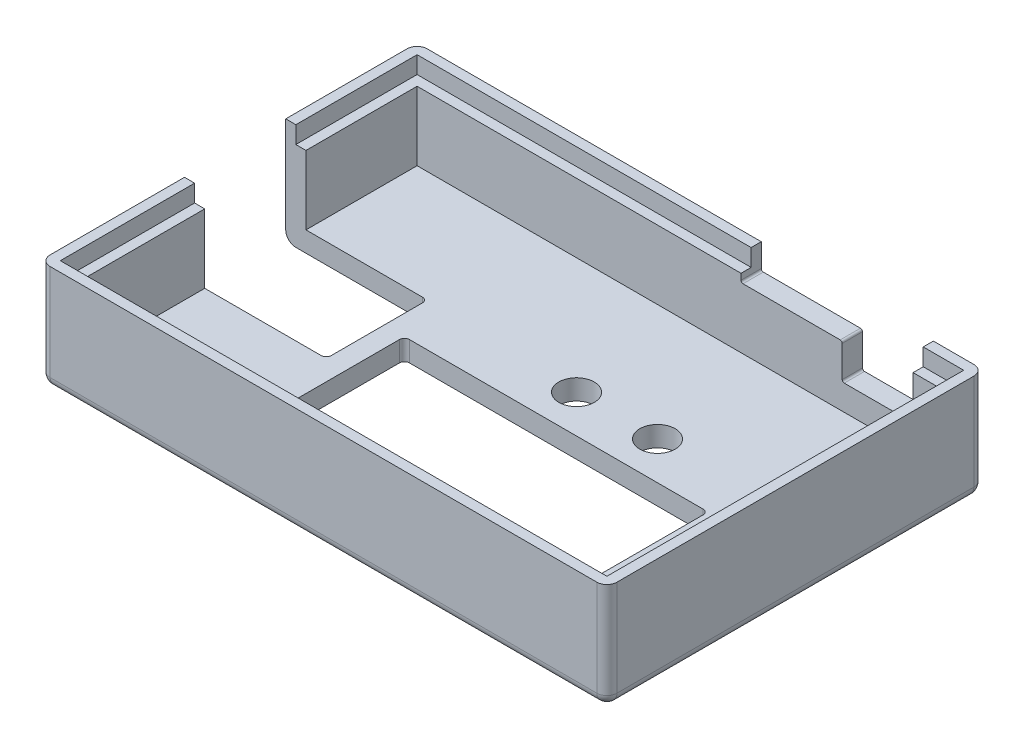
SolidWorks part; units mm, degrees
ref_plane "Front Plane" through (0, 0, 0) normal (0, 0, 1) x (1, 0, 0)
ref_plane "Top Plane" through (0, 0, 0) normal (0, 1, 0) x (1, 0, 0)
ref_plane "Right Plane" through (0, 0, 0) normal (1, 0, 0) x (0, 0, -1)
sketch "Sketch1" plane through (0, 0, 0) normal (0, 1, 0) x (1, 0, 0)
  line L0 (0, 0) -> (56, 0)
  line L1 (56, 0) -> (56, 37.25)
  line L2 (56, 37.25) -> (0, 37.25)
  line L3 (0, 37.25) -> (0, 0)
  dimension "D1" = 56
  dimension "D2" = 37.25
extrude "Boss-Extrude1" add sketch "Sketch1" along normal blind 2
sketch "Sketch2" plane through (0, 2, 0) normal (0, 1, 0) x (1, 0, 0)
  line L0 (2, 35.25) -> (2, 2)
  line L1 (2, 2) -> (54, 2)
  line L2 (0, 37.25) -> (0, 0) construction
  line L3 (0, 0) -> (56, 0) construction
  line L4 (2, 35.25) -> (54, 35.25)
  line L5 (54, 35.25) -> (54, 2)
  line L6 (56, 0) -> (56, 37.25) construction
  line L7 (56, 37.25) -> (0, 37.25) construction
  line L12 (0, 37.25) -> (0, 0)
  line L13 (0, 0) -> (56, 0)
  line L14 (56, 0) -> (56, 37.25)
  line L15 (56, 37.25) -> (0, 37.25)
  line L16 (0, 37.25) -> (0, 0)
  line L17 (0, 0) -> (56, 0)
  line L18 (56, 0) -> (56, 37.25)
  line L19 (56, 37.25) -> (0, 37.25)
  dimension "D1" = 2
  dimension "D2" = 2
  dimension "D3" = 2
  dimension "D4" = 2
  dimension "D5" = 0
extrude "Boss-Extrude2" add sketch "Sketch2" along normal blind 8.5
sketch "Sketch3" plane through (0, 2, 0) normal (0, 1, 0) x (1, 0, 0)
  line L0 (54, 2) -> (54, 35.25) construction
  line L4 (2, 18.625) -> (54, 18.625) construction
  line L5 (2, 35.25) -> (2, 2) construction
  line L6 (12, 6) -> (48, 6) construction
  line L7 (12, 32) -> (12, 6) construction
  circle A0 centre (12, 32) radius 1.6
  circle A1 centre (12, 6) radius 1.6
  circle A2 centre (48, 6) radius 1.6
  circle A6 centre (48, 6) radius 1.5 construction
  circle A7 centre (12, 6) radius 1.5 construction
  circle A8 centre (12, 32) radius 1.5 construction
  circle A9 centre (48, 6) radius 2 construction
  circle A10 centre (12, 6) radius 2 construction
  circle A11 centre (12, 32) radius 2 construction
sketch "Sketch5" plane through (0, 10.5, 0) normal (0, 1, 0) x (1, 0, 0)
  line L0 (1, 1) -> (55, 1)
  line L1 (0, 0) -> (56, 0) construction
  line L2 (55, 1) -> (55, 36.25)
  line L3 (55, 36.25) -> (1, 36.25)
  line L4 (1, 36.25) -> (1, 1)
  line L5 (56, 0) -> (56, 37.25) construction
  line L6 (56, 37.25) -> (0, 37.25) construction
  line L7 (0, 37.25) -> (0, 0) construction
  line L8 (0, 37.25) -> (0, 0)
  line L9 (56, 37.25) -> (0, 37.25)
  line L10 (56, 0) -> (56, 37.25)
  line L11 (0, 0) -> (56, 0)
  line L12 (54, 2) -> (54, 35.25) construction
  line L13 (54, 35.25) -> (2, 35.25) construction
  line L14 (2, 35.25) -> (2, 2) construction
  line L15 (2, 2) -> (54, 2) construction
  line L16 (54, 2) -> (54, 35.25)
  line L17 (54, 35.25) -> (2, 35.25)
  line L18 (2, 35.25) -> (2, 2)
  line L19 (2, 2) -> (54, 2)
  line M9 (2, 2) -> (2, 35.25)
  line M10 (2, 35.25) -> (54, 35.25)
  line M11 (54, 35.25) -> (54, 2)
  line M12 (54, 2) -> (2, 2)
  dimension "D1" = 1
  dimension "D2" = 1
  dimension "D3" = 1
  dimension "D4" = 1
extrude "Cut-Extrude1" cut sketch "Sketch5" against normal blind 1 contours L3 L4 L0 L2 M12 M9 M10 M11 | L18 L19 L16 L17
fillet "Fillet1" radius 1 4 edges at (56, 5.25, -37.25) (56, 5.25, 0) (0, 5.25, -37.25) (0, 5.25, 0)
extrude "Cut-Extrude2" [suppressed] cut sketch "Sketch3" against normal blind 10
sketch "Sketch7" plane through (0, 2, 0) normal (0, 1, 0) x (1, 0, 0)
  line L0 (16, 6) -> (46, 6)
  line L1 (46, 6) -> (46, 20)
  line L2 (16, 6) -> (16, 20)
  line L3 (16, 20) -> (46, 20)
  line L4 (54, 2) -> (54, 35.25) construction
  line L6 (2, 2) -> (54, 2) construction
  dimension "D1" = 14
  dimension "D2" = 30
  dimension "D3" = 8
  dimension "D4" = 4
extrude "Cut-Extrude3" cut sketch "Sketch7" against normal blind 10
sketch "Sketch8" plane through (0, 0, 0) normal (0, -1, 0) x (1, 0, 0)
  circle A0 centre (29.25, -23.75) radius 1.75
  circle A1 centre (37.25, -23.75) radius 1.75
extrude "Cut-Extrude4" cut sketch "Sketch8" against normal blind 10
sketch "Sketch9" plane through (0, 0, -37.25) normal (0, 0, -1) x (-1, 0, 0)
  line L0 (-44, 4.5) -> (-44, 10.5)
  line L1 (-44, 10.5) -> (-51, 10.5)
  line L2 (-51, 10.5) -> (-51, 4.5)
  line L3 (-51, 4.5) -> (-44, 4.5)
  line L4 (-55, 10.5) -> (-55, 0) construction
  line L5 (-55, 10.5) -> (-1, 10.5) construction
  point P5 (-55, 5.25)
  dimension "D1" = 7
  dimension "D2" = 6
  dimension "D3" = 4
  dimension "D4" = 0
extrude "Cut-Extrude5" cut sketch "Sketch9" against normal blind 3
sketch "Sketch10" plane through (0, 0, -37.25) normal (0, 0, -1) x (-1, 0, 0)
  line L0 (-44, 10.5) -> (-44, 8)
  line L1 (-55, 10.5) -> (-51, 10.5) construction
  line L2 (-44, 8) -> (-34, 8)
  line L3 (-34, 8) -> (-34, 10.5)
  line L4 (-55, 10.5) -> (-55, 0) construction
  line L5 (-34, 10.5) -> (-44, 10.5)
  dimension "D1" = 10
  dimension "D2" = 2.5
  dimension "D3" = 11
extrude "Cut-Extrude6" cut sketch "Sketch10" against normal blind 3
fillet "Fillet2" radius 0.5 4 edges at (46, 1, -20) (16, 1, -20) (16, 1, -6) (46, 1, -6)
sketch "Sketch11" plane through (0, 0, 0) normal (0, -1, 0) x (1, 0, 0)
  line L0 (0, -24.271) -> (14, -24.271)
  line L1 (0, -36.25) -> (0, -1) construction
  line L2 (14, -24.271) -> (14, -14.271)
  line L3 (14, -14.271) -> (0, -14.271)
  line L4 (0, -14.271) -> (0, -24.271)
  line L5 (1, 0) -> (55, 0) construction
  dimension "D1" = 14
  dimension "D2" = 10
  dimension "D3" = 14.271
extrude "Cut-Extrude7" cut sketch "Sketch11" against normal through all
fillet "Fillet3" radius 1 8 edges at (0, 0, -30.2605) (0.2929, 0, -0.2929) (28, 0, 0) (55.7071, 0, -0.2929) (56, 0, -18.625) (55.7071, 0, -36.9571) (0.2929, 0, -36.9571) (28, 0, -37.25)
fillet "Fillet4" radius 0.5 2 edges at (14, 1, -14.271) (14, 1, -24.271)
fillet "Fillet5" radius 0.2 4 edges at (34, 8, -36.25) (44, 8, -36.25) (51, 4.5, -36.25) (44, 4.5, -36.25)
sketch "Sketch12" plane through (0, 9.5, 0) normal (0, 1, 0) x (1, 0, 0)
  line L6 (1, 24.271) -> (2, 24.271)
  line L7 (2, 24.271) -> (2, 35.25)
  line L8 (2, 35.25) -> (34, 35.25)
  line L9 (34, 35.25) -> (34, 36.25)
  line L10 (2, 14.271) -> (1, 14.271)
  line L11 (1, 14.271) -> (1, 1)
  line L12 (1, 1) -> (55, 1)
  line L13 (55, 1) -> (55, 36.25)
  line L14 (55, 36.25) -> (51, 36.25)
  line L15 (51, 36.25) -> (51, 35.25)
  line L16 (51, 35.25) -> (54, 35.25)
  line L17 (54, 35.25) -> (54, 2)
  line L18 (54, 2) -> (2, 2)
  line L19 (2, 2) -> (2, 14.271)
  line L20 (2, 14.271) -> (1, 14.271)
  line L21 (1, 14.271) -> (1, 1)
  line L22 (1, 1) -> (55, 1)
  line L23 (55, 1) -> (55, 36.25)
  line L24 (55, 36.25) -> (51, 36.25)
  line L25 (51, 36.25) -> (51, 35.25)
  line L26 (51, 35.25) -> (54, 35.25)
  line L27 (54, 35.25) -> (54, 2)
  line L28 (54, 2) -> (2, 2)
  line L29 (2, 2) -> (2, 14.271)
  line L30 (34, 36.25) -> (1, 36.25)
  line L31 (1, 36.25) -> (1, 24.271)
  line L32 (1, 24.271) -> (2, 24.271)
  line L33 (2, 24.271) -> (2, 35.25)
  line L34 (2, 35.25) -> (34, 35.25)
  line L35 (34, 35.25) -> (34, 36.25)
  line L36 (34, 36.25) -> (1, 36.25)
  line L37 (1, 36.25) -> (1, 24.271)
  dimension "D1" = 0
  dimension "D2" = 0
extrude "Cut-Extrude8" cut sketch "Sketch12" against normal blind 0.7
